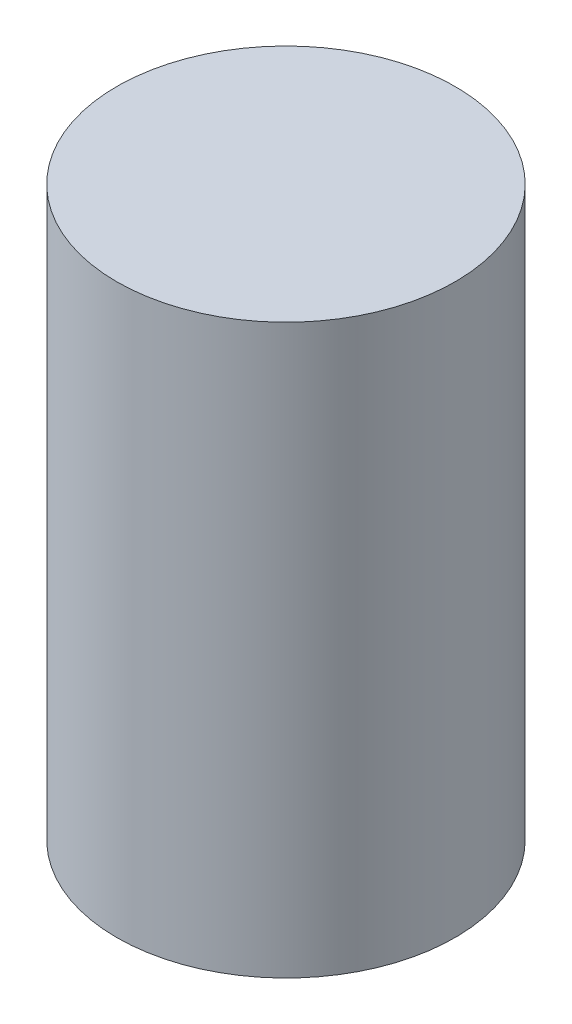
SolidWorks part; units mm, degrees
ref_plane "Front Plane" through (0, 0, 0) normal (0, 0, 1) x (1, 0, 0)
ref_plane "Top Plane" through (0, 0, 0) normal (0, 1, 0) x (1, 0, 0)
ref_plane "Right Plane" through (0, 0, 0) normal (1, 0, 0) x (0, 0, -1)
other "Bounding Box"
ref_plane "Default Plane" through (-8.9266, -12.7485, 0) normal (-0.1736, 0.9848, 0) x (0.9848, 0.1736, 0)
sketch "Sketch1" plane through (0, 0, 0) normal (0, 1, 0) x (1, 0, 0)
  circle A0 centre (0, 0) radius 14
  dimension "D1" = 28
extrude "Boss-Extrude1" add sketch "Sketch1" along normal mid plane 47
